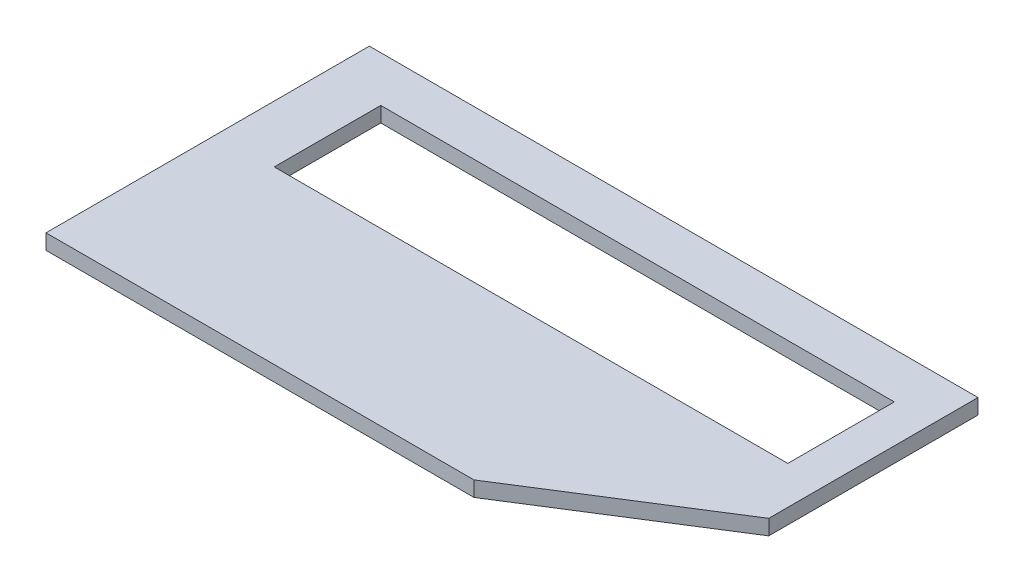
SolidWorks part; units mm, degrees
ref_plane "Спереди" through (0, 0, 0) normal (0, 0, 1) x (1, 0, 0)
ref_plane "Сверху" through (0, 0, 0) normal (0, 1, 0) x (1, 0, 0)
ref_plane "Справа" through (0, 0, 0) normal (1, 0, 0) x (0, 0, -1)
sketch "Эскиз1" plane through (0, 0, 0) normal (0, 1, 0) x (1, 0, 0)
  line L0 (320, 170) -> (320, 60)
  line L1 (0, 0) -> (225, 0)
  line L2 (0, 0) -> (0, 170)
  line L3 (0, 170) -> (320, 170)
  line L5 (320, 60) -> (225, 0)
  line L7 (30, 146) -> (300, 146)
  line L8 (30, 146) -> (30, 90)
  line L9 (30, 90) -> (300, 90)
  line L10 (300, 146) -> (300, 90)
  point P5 (0, 0)
  point P6 (0, 0)
  point P8 (0, 0)
  dimension "D1" = 95
  dimension "D2" = 110
extrude "Бобышка-Вытянуть1" add sketch "Эскиз1" along normal blind 8
